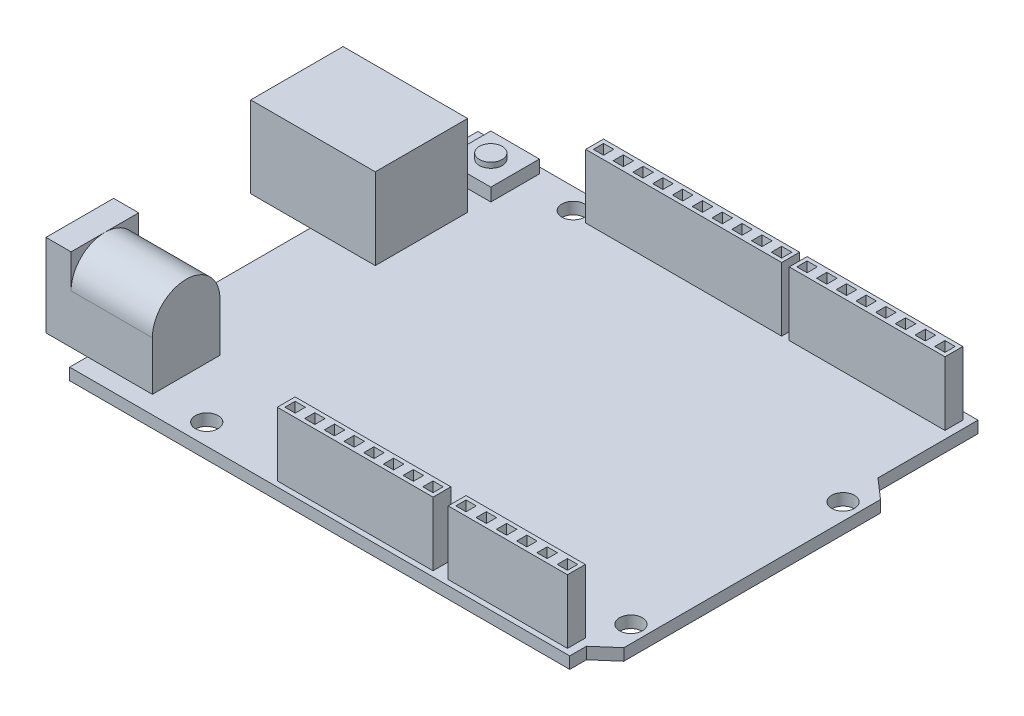
SolidWorks part; units mm, degrees
ref_plane "Plano frontal" through (0, 0, 0) normal (0, 0, 1) x (1, 0, 0)
ref_plane "Plano superior" through (0, 0, 0) normal (0, 1, 0) x (1, 0, 0)
ref_plane "Plano direito" through (0, 0, 0) normal (1, 0, 0) x (0, 0, -1)
sketch "Esboço1" plane through (0, 0, 0) normal (0, 1, 0) x (1, 0, 0)
  line L0 (-32.92, 26.875) -> (32.92, 26.875)
  line L1 (-32.92, 26.875) -> (-32.92, -26.875)
  line L2 (-32.92, -26.875) -> (32.92, -26.875)
  line L3 (32.92, -26.875) -> (32.92, -24.675)
  line L4 (32.92, -24.675) -> (35.55, -22.3808)
  line L5 (35.55, -22.3808) -> (35.55, 11.4108)
  line L6 (35.55, 11.4108) -> (32.92, 13.705)
  line L7 (32.92, 13.705) -> (32.92, 26.875)
  line L8 (32.92, -26.875) -> (-32.92, 26.875) construction
  line L9 (32.92, 26.875) -> (-32.92, -26.875) construction
  point P2 (35.55, -23.3319)
  point P9 (35.55, -23.2011)
  dimension "D1" = 53.75
  dimension "D2" = 65.84
  dimension "D3" = 38.38
  dimension "D4" = 68.47
  dimension "D5" = 3.49
  dimension "D6" = 2.2
  dimension "D7" = 33.7917
extrude "Ressalto-extrusão1" add sketch "Esboço1" along normal mid plane 1.55
sketch "Esboço2" plane through (0, 0.775, 0) normal (0, 1, 0) x (1, 0, 0)
  line L0 (32.92, 26.875) -> (-32.92, 26.875) construction
  line L1 (-40.77, 16.975) -> (-24.37, 16.975)
  line L2 (-40.77, 16.975) -> (-40.77, 4.815)
  line L3 (-40.77, 4.815) -> (-24.37, 4.815)
  line L4 (-24.37, 16.975) -> (-24.37, 4.815)
  line L5 (-32.92, 26.875) -> (-32.92, -26.875) construction
  dimension "D1" = 16.4
  dimension "D2" = 12.16
  dimension "D3" = 9.9
  dimension "D4" = 7.85
extrude "Ressalto-extrusão2" add sketch "Esboço2" along normal blind 10.7
sketch "Esboço3" plane through (0, 0.775, 0) normal (0, 1, 0) x (1, 0, 0)
  line L0 (-32.92, 26.875) -> (-32.92, 16.975) construction
  line L1 (-30.42, 26.075) -> (-24.02, 26.075)
  line L2 (-30.42, 26.075) -> (-30.42, 19.675)
  line L3 (-30.42, 19.675) -> (-24.02, 19.675)
  line L4 (-24.02, 26.075) -> (-24.02, 19.675)
  line L5 (32.92, 26.875) -> (-32.92, 26.875) construction
  point P4 (-31.1778, 18.6624)
  dimension "D1" = 6.4
  dimension "D2" = 2.5
  dimension "D3" = 0.8
extrude "Ressalto-extrusão3" add sketch "Esboço3" along normal blind 1.7
sketch "Esboço4" plane through (0, 2.475, 0) normal (0, 1, 0) x (1, 0, 0)
  line L0 (-30.42, 26.075) -> (-24.02, 19.675) construction
  circle A0 centre (-27.22, 22.875) radius 1.5
  point P6 (0, 0)
  dimension "D1" = 3
extrude "Ressalto-extrusão4" add sketch "Esboço4" along normal blind 0.7 separate body
sketch "Esboço5" plane through (0, 0.775, 0) normal (0, 1, 0) x (1, 0, 0)
  line L1 (-38.37, -24.535) -> (-24.37, -24.535)
  line L2 (-38.37, -24.535) -> (-38.37, -15.635)
  line L3 (-38.37, -15.635) -> (-24.37, -15.635)
  line L4 (-24.37, -24.535) -> (-24.37, -15.635)
  line L5 (-32.92, 4.815) -> (-32.92, -26.875) construction
  line L6 (-32.92, -26.875) -> (32.92, -26.875) construction
  dimension "D1" = 8.9
  dimension "D2" = 14
  dimension "D3" = 8.55
  dimension "D4" = 2.34
extrude "Ressalto-extrusão5" add sketch "Esboço5" along normal blind 10.9 separate body
sketch "Esboço6" plane through (-24.37, 0, 0) normal (1, 0, 0) x (0, 0, -1)
  line L0 (-24.535, 11.675) -> (-15.635, 11.675) construction
  line L1 (-24.535, 11.675) -> (-24.535, 0.775) construction
  line L2 (-15.635, 11.675) -> (-15.635, 0.775) construction
  line L8 (-24.535, 7.225) -> (-25.535, 7.225)
  line L9 (-25.535, 7.225) -> (-25.535, 12.675)
  line L10 (-25.535, 12.675) -> (-14.635, 12.675)
  line L11 (-14.635, 12.675) -> (-14.635, 7.225)
  line L12 (-14.635, 7.225) -> (-15.635, 7.225)
  arc A0 (-15.635, 7.225) -> (-24.535, 7.225) centre (-20.085, 7.225) ccw
  point P6 (-14.635, 7.225)
  dimension "D2" = 1
  dimension "D1" = 1
extrude "Corte-extrusão1" cut sketch "Esboço6" against normal offset from surface (10.7 mm away) 3.3 up to face at (-38.37, 6.225, 20.085)
sketch "Esboço7" plane through (0, 0.775, 0) normal (0, 1, 0) x (1, 0, 0)
  line L0 (32.92, -26.875) -> (32.92, -24.675) construction
  line L1 (-15.38, 25.875) -> (10.42, 25.875)
  line L2 (-15.38, 25.875) -> (-15.38, 23.525)
  line L3 (-15.38, 23.525) -> (10.42, 23.525)
  line L4 (10.42, 25.875) -> (10.42, 23.525)
  line L5 (11.42, 25.875) -> (31.92, 25.875)
  line L6 (11.42, 25.875) -> (11.42, 23.525)
  line L7 (11.42, 23.525) -> (31.92, 23.525)
  line L8 (31.92, 25.875) -> (31.92, 23.525)
  line L9 (-6.28, -23.825) -> (14.22, -23.825)
  line L10 (-6.28, -23.825) -> (-6.28, -26.175)
  line L11 (-6.28, -26.175) -> (14.22, -26.175)
  line L12 (14.22, -23.825) -> (14.22, -26.175)
  line L13 (16.22, -23.825) -> (31.92, -23.825)
  line L14 (16.22, -23.825) -> (16.22, -26.175)
  line L15 (16.22, -26.175) -> (31.92, -26.175)
  line L16 (31.92, -23.825) -> (31.92, -26.175)
  line L17 (32.92, 26.875) -> (-32.92, 26.875) construction
  line L18 (-32.92, -26.875) -> (32.92, -26.875) construction
  dimension "D1" = 2
  dimension "D2" = 1
  dimension "D3" = 2.35
  dimension "D4" = 15.7
  dimension "D5" = 20.5
  dimension "D6" = 20.5
  dimension "D7" = 25.8
  dimension "D8" = 1
  dimension "D9" = 1
  dimension "D10" = 0.7
extrude "Ressalto-extrusão6" add sketch "Esboço7" along normal blind 8.4 separate body
sketch "Esboço8" plane through (0, -0.775, 0) normal (0, -1, 0) x (1, 0, 0)
  line L3 (32.92, -26.875) -> (-32.92, -26.875) construction
  line L4 (-32.92, 26.875) -> (32.92, 26.875) construction
  line L9 (35.55, 22.3808) -> (35.55, -11.4108) construction
  line L11 (-32.92, -26.875) -> (-32.92, 26.875) construction
  circle A0 centre (-17.62, 24.125) radius 1.5
  circle A1 centre (-17.62, -24.125) radius 1.5
  circle A2 centre (33.35, -8.675) radius 1.5
  circle A3 centre (33.35, 19.245) radius 1.5
  point P8 (0, 0)
  point P9 (0, 0)
  dimension "D1" = 3
  dimension "D2" = 2.75
  dimension "D4" = 6.13
  dimension "D5" = 16.7
  dimension "D6" = 0.7
  dimension "D7" = 13.8
  dimension "D3" = 2.75
extrude "Corte-extrusão2" cut sketch "Esboço8" against normal through all and the other way through all
sketch "Esboço9" plane through (0, 9.175, 0) normal (0, 1, 0) x (1, 0, 0)
  line L0 (-15.38, 25.875) -> (-15.38, 23.525) construction
  line L1 (-14.88, 24.025) -> (-13.53, 24.025)
  line L2 (-14.88, 24.025) -> (-14.88, 25.375)
  line L3 (-14.88, 25.375) -> (-13.53, 25.375)
  line L4 (-13.53, 24.025) -> (-13.53, 25.375)
  line L5 (-14.88, 24.025) -> (-13.53, 25.375) construction
  line L6 (-14.88, 25.375) -> (-13.53, 24.025) construction
  line L7 (10.42, 25.875) -> (-15.38, 25.875) construction
  line L8 (-15.38, 23.525) -> (10.42, 23.525) construction
  line L9 (-12.2744, 24.025) -> (-12.2744, 25.375)
  line L10 (-12.2744, 24.025) -> (-10.9244, 24.025)
  line L11 (-10.9244, 24.025) -> (-10.9244, 25.375)
  line L12 (-12.2744, 25.375) -> (-10.9244, 25.375)
  line L13 (-14.88, 24.025) -> (-12.2744, 24.025) construction
  line L14 (-9.6689, 24.025) -> (-9.6689, 25.375)
  line L15 (-9.6689, 24.025) -> (-8.3189, 24.025)
  line L16 (-8.3189, 24.025) -> (-8.3189, 25.375)
  line L17 (-9.6689, 25.375) -> (-8.3189, 25.375)
  line L18 (-7.0633, 24.025) -> (-7.0633, 25.375)
  line L19 (-7.0633, 24.025) -> (-5.7133, 24.025)
  line L20 (-5.7133, 24.025) -> (-5.7133, 25.375)
  line L21 (-7.0633, 25.375) -> (-5.7133, 25.375)
  line L22 (-4.4578, 24.025) -> (-4.4578, 25.375)
  line L23 (-4.4578, 24.025) -> (-3.1078, 24.025)
  line L24 (-3.1078, 24.025) -> (-3.1078, 25.375)
  line L25 (-4.4578, 25.375) -> (-3.1078, 25.375)
  line L26 (-1.8522, 24.025) -> (-1.8522, 25.375)
  line L27 (-1.8522, 24.025) -> (-0.5022, 24.025)
  line L28 (-0.5022, 24.025) -> (-0.5022, 25.375)
  line L29 (-1.8522, 25.375) -> (-0.5022, 25.375)
  line L30 (0.7533, 24.025) -> (0.7533, 25.375)
  line L31 (0.7533, 24.025) -> (2.1033, 24.025)
  line L32 (2.1033, 24.025) -> (2.1033, 25.375)
  line L33 (0.7533, 25.375) -> (2.1033, 25.375)
  line L34 (3.3589, 24.025) -> (3.3589, 25.375)
  line L35 (3.3589, 24.025) -> (4.7089, 24.025)
  line L36 (4.7089, 24.025) -> (4.7089, 25.375)
  line L37 (3.3589, 25.375) -> (4.7089, 25.375)
  line L38 (5.9644, 24.025) -> (5.9644, 25.375)
  line L39 (5.9644, 24.025) -> (7.3144, 24.025)
  line L40 (7.3144, 24.025) -> (7.3144, 25.375)
  line L41 (5.9644, 25.375) -> (7.3144, 25.375)
  line L42 (8.57, 24.025) -> (8.57, 25.375)
  line L43 (8.57, 24.025) -> (9.92, 24.025)
  line L44 (9.92, 24.025) -> (9.92, 25.375)
  line L45 (8.57, 25.375) -> (9.92, 25.375)
  line L46 (10.42, 23.525) -> (10.42, 25.875) construction
  line L47 (11.92, 24.025) -> (13.27, 24.025)
  line L48 (11.92, 24.025) -> (11.92, 25.375)
  line L49 (11.92, 25.375) -> (13.27, 25.375)
  line L50 (13.27, 24.025) -> (13.27, 25.375)
  line L51 (-5.78, -25.675) -> (-4.43, -25.675)
  line L52 (-5.78, -25.675) -> (-5.78, -24.325)
  line L53 (-5.78, -24.325) -> (-4.43, -24.325)
  line L54 (-4.43, -25.675) -> (-4.43, -24.325)
  line L55 (16.72, -25.675) -> (18.07, -25.675)
  line L56 (16.72, -25.675) -> (16.72, -24.325)
  line L57 (16.72, -24.325) -> (18.07, -24.325)
  line L58 (18.07, -25.675) -> (18.07, -24.325)
  line L59 (-6.28, -23.825) -> (-6.28, -26.175) construction
  line L60 (14.22, -23.825) -> (-6.28, -23.825) construction
  line L61 (31.92, -23.825) -> (16.22, -23.825) construction
  line L62 (16.22, -23.825) -> (16.22, -26.175) construction
  line L63 (31.92, 25.875) -> (11.42, 25.875) construction
  line L64 (11.42, 25.875) -> (11.42, 23.525) construction
  line L65 (14.5129, 24.025) -> (15.8629, 24.025)
  line L66 (15.8629, 24.025) -> (15.8629, 25.375)
  line L67 (14.5129, 25.375) -> (15.8629, 25.375)
  line L68 (14.5129, 24.025) -> (14.5129, 25.375)
  line L69 (17.1057, 24.025) -> (18.4557, 24.025)
  line L70 (18.4557, 24.025) -> (18.4557, 25.375)
  line L71 (17.1057, 25.375) -> (18.4557, 25.375)
  line L72 (17.1057, 24.025) -> (17.1057, 25.375)
  line L73 (19.6986, 24.025) -> (21.0486, 24.025)
  line L74 (21.0486, 24.025) -> (21.0486, 25.375)
  line L75 (19.6986, 25.375) -> (21.0486, 25.375)
  line L76 (19.6986, 24.025) -> (19.6986, 25.375)
  line L77 (22.2914, 24.025) -> (23.6414, 24.025)
  line L78 (23.6414, 24.025) -> (23.6414, 25.375)
  line L79 (22.2914, 25.375) -> (23.6414, 25.375)
  line L80 (22.2914, 24.025) -> (22.2914, 25.375)
  line L81 (24.8843, 24.025) -> (26.2343, 24.025)
  line L82 (26.2343, 24.025) -> (26.2343, 25.375)
  line L83 (24.8843, 25.375) -> (26.2343, 25.375)
  line L84 (24.8843, 24.025) -> (24.8843, 25.375)
  line L85 (27.4771, 24.025) -> (28.8271, 24.025)
  line L86 (28.8271, 24.025) -> (28.8271, 25.375)
  line L87 (27.4771, 25.375) -> (28.8271, 25.375)
  line L88 (27.4771, 24.025) -> (27.4771, 25.375)
  line L89 (30.07, 24.025) -> (31.42, 24.025)
  line L90 (31.42, 24.025) -> (31.42, 25.375)
  line L91 (30.07, 25.375) -> (31.42, 25.375)
  line L92 (30.07, 24.025) -> (30.07, 25.375)
  line L93 (11.92, 24.025) -> (14.5129, 24.025) construction
  line L94 (31.92, 23.525) -> (31.92, 25.875) construction
  line L95 (-3.1871, -25.675) -> (-1.8371, -25.675)
  line L96 (-1.8371, -25.675) -> (-1.8371, -24.325)
  line L97 (-3.1871, -24.325) -> (-1.8371, -24.325)
  line L98 (-3.1871, -25.675) -> (-3.1871, -24.325)
  line L99 (-0.5943, -25.675) -> (0.7557, -25.675)
  line L100 (0.7557, -25.675) -> (0.7557, -24.325)
  line L101 (-0.5943, -24.325) -> (0.7557, -24.325)
  line L102 (-0.5943, -25.675) -> (-0.5943, -24.325)
  line L103 (1.9986, -25.675) -> (3.3486, -25.675)
  line L104 (3.3486, -25.675) -> (3.3486, -24.325)
  line L105 (1.9986, -24.325) -> (3.3486, -24.325)
  line L106 (1.9986, -25.675) -> (1.9986, -24.325)
  line L107 (4.5914, -25.675) -> (5.9414, -25.675)
  line L108 (5.9414, -25.675) -> (5.9414, -24.325)
  line L109 (4.5914, -24.325) -> (5.9414, -24.325)
  line L110 (4.5914, -25.675) -> (4.5914, -24.325)
  line L111 (7.1843, -25.675) -> (8.5343, -25.675)
  line L112 (8.5343, -25.675) -> (8.5343, -24.325)
  line L113 (7.1843, -24.325) -> (8.5343, -24.325)
  line L114 (7.1843, -25.675) -> (7.1843, -24.325)
  line L115 (9.7771, -25.675) -> (11.1271, -25.675)
  line L116 (11.1271, -25.675) -> (11.1271, -24.325)
  line L117 (9.7771, -24.325) -> (11.1271, -24.325)
  line L118 (9.7771, -25.675) -> (9.7771, -24.325)
  line L119 (12.37, -25.675) -> (13.72, -25.675)
  line L120 (13.72, -25.675) -> (13.72, -24.325)
  line L121 (12.37, -24.325) -> (13.72, -24.325)
  line L122 (12.37, -25.675) -> (12.37, -24.325)
  line L123 (19.39, -25.675) -> (20.74, -25.675)
  line L124 (20.74, -25.675) -> (20.74, -24.325)
  line L125 (19.39, -24.325) -> (20.74, -24.325)
  line L126 (19.39, -25.675) -> (19.39, -24.325)
  line L127 (22.06, -25.675) -> (23.41, -25.675)
  line L128 (23.41, -25.675) -> (23.41, -24.325)
  line L129 (22.06, -24.325) -> (23.41, -24.325)
  line L130 (22.06, -25.675) -> (22.06, -24.325)
  line L131 (24.73, -25.675) -> (26.08, -25.675)
  line L132 (26.08, -25.675) -> (26.08, -24.325)
  line L133 (24.73, -24.325) -> (26.08, -24.325)
  line L134 (24.73, -25.675) -> (24.73, -24.325)
  line L135 (27.4, -25.675) -> (28.75, -25.675)
  line L136 (28.75, -25.675) -> (28.75, -24.325)
  line L137 (27.4, -24.325) -> (28.75, -24.325)
  line L138 (27.4, -25.675) -> (27.4, -24.325)
  line L139 (30.07, -25.675) -> (31.42, -25.675)
  line L140 (31.42, -25.675) -> (31.42, -24.325)
  line L141 (30.07, -24.325) -> (31.42, -24.325)
  line L142 (30.07, -25.675) -> (30.07, -24.325)
  line L143 (14.22, -26.175) -> (14.22, -23.825) construction
  line L144 (31.92, -26.175) -> (31.92, -23.825) construction
  point P0 (-14.205, 24.7)
  point P72 (16.22, -25)
  dimension "D1" = 0.5
  dimension "D2" = 0.5
  dimension "D3" = 0.5
  dimension "D4" = 10
  dimension "D5" = 0.5
  dimension "D6" = 0.5
  dimension "D7" = 0.5
  dimension "D8" = 0.5
  dimension "D9" = 0.5
  dimension "D10" = 0.5
  dimension "D11" = 0.5
  dimension "D13" = 0.5
  dimension "D16" = 0.5
  dimension "D17" = 0.5
  dimension "D12" = 8
  dimension "D14" = 8
  dimension "D15" = 6
extrude "Corte-extrusão3" cut sketch "Esboço9" against normal blind 5 draft 5
